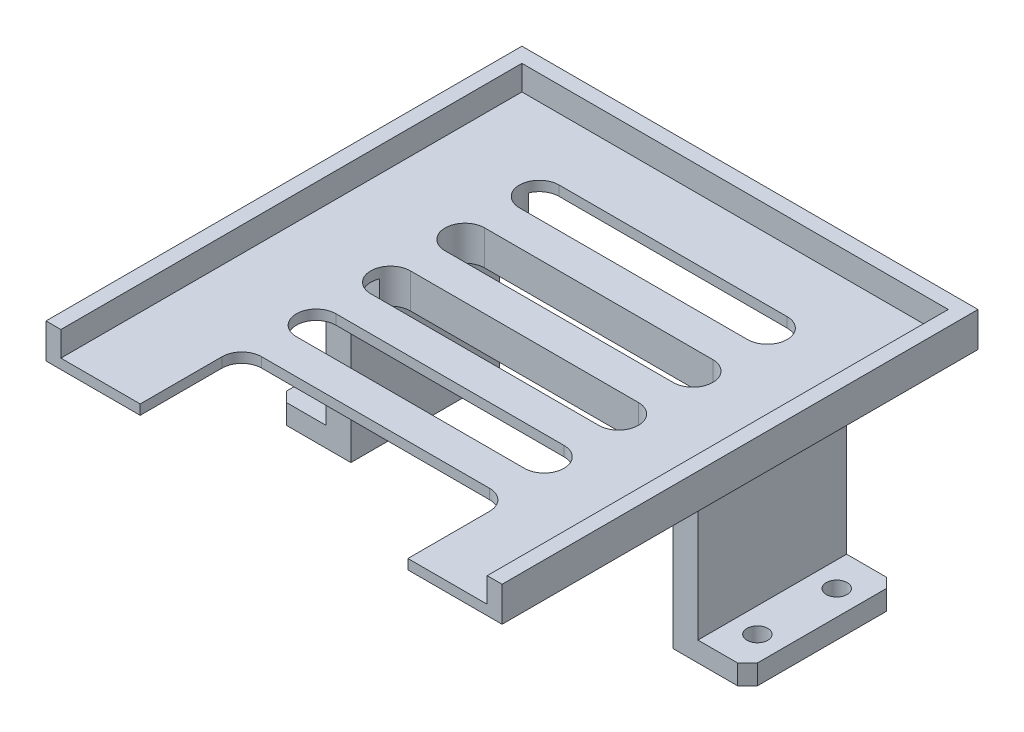
SolidWorks part; units mm, degrees
ref_plane "Front Plane" through (0, 0, 0) normal (0, 0, 1) x (1, 0, 0)
ref_plane "Top Plane" through (0, 0, 0) normal (0, 1, 0) x (1, 0, 0)
ref_plane "Right Plane" through (0, 0, 0) normal (1, 0, 0) x (0, 0, -1)
sketch "Sketch1" plane through (0, 0, 0) normal (0, 0, 1) x (1, 0, 0)
  line L0 (0, 17.5) -> (0, -17.5) construction
  line L1 (-37.5, -17.5) -> (37.5, -17.5)
  line L2 (-37.5, -12.5) -> (-37.5, 17.5)
  line L3 (-37.5, 17.5) -> (37.5, 17.5)
  line L4 (37.5, -12.5) -> (37.5, 17.5)
  line L5 (-37.5, -17.5) -> (37.5, 17.5) construction
  line L6 (-37.5, 17.5) -> (37.5, -17.5) construction
  line L7 (-37.5, -12.5) -> (-57.5, -12.5)
  line L8 (-32.5, -17.5) -> (32.5, -17.5)
  line L9 (-32.5, -17.5) -> (-32.5, 12.5)
  line L10 (-32.5, 12.5) -> (32.5, 12.5)
  line L11 (32.5, -17.5) -> (32.5, 12.5)
  line L12 (37.5, -17.5) -> (57.5, -17.5)
  line L14 (37.5, -12.5) -> (57.5, -12.5)
  line L15 (57.5, -17.5) -> (57.5, -12.5)
  line L16 (-57.5, -17.5) -> (-57.5, -12.5)
  line L17 (-37.5, -17.5) -> (-57.5, -17.5)
  point P0 (0, 0)
  dimension "D1" = 35
  dimension "D2" = 75
  dimension "D3" = 5
  dimension "D4" = 5
  dimension "D5" = 5
  dimension "D6" = 5
  dimension "D7" = 20
extrude "Boss-Extrude1" add sketch "Sketch1" along normal blind 30 contours L17 L1 L9 L10 L11 L12 L15 L14 L4 L3 L2 L7 L16
sketch "Sketch2" plane through (0, 17.5, 0) normal (0, 1, 0) x (1, 0, 0)
  line L0 (-37.5, -15) -> (37.5, -15) construction
  line L1 (-37.5, -30) -> (-37.5, 0) construction
  line L2 (37.5, -30) -> (37.5, 0) construction
  line L3 (0, 0) -> (0, -30) construction
  line L4 (-37.5, -30) -> (37.5, -30) construction
  line L6 (-25, -25) -> (25, -25)
  line L7 (-25, -25) -> (-25, -5)
  line L8 (-25, -5) -> (25, -5)
  line L9 (25, -25) -> (25, -5)
  line L10 (-25, -25) -> (25, -5) construction
  line L11 (-25, -5) -> (25, -25) construction
  point P11 (0, -15)
  dimension "D1" = 50
  dimension "D2" = 20
extrude "Cut-Extrude1" cut sketch "Sketch2" against normal blind 30
chamfer "Chamfer1" distance 2 angle 45 2 edges at (37.5, 17.5, 15) (-37.5, 17.5, 15)
sketch "Sketch3" plane through (0, -12.5, 0) normal (0, 1, 0) x (1, 0, 0)
  line L0 (-47.5, 0) -> (-47.5, -30) construction
  line L1 (-37.5, 0) -> (-57.5, 0) construction
  line L2 (-37.5, -30) -> (-57.5, -30) construction
  line L3 (47.5, 0) -> (47.5, -30) construction
  line L4 (37.5, 0) -> (57.5, 0) construction
  line L5 (37.5, -30) -> (57.5, -30) construction
  circle A0 centre (-47.5, -15) radius 2.1
  circle A1 centre (47.5, -15) radius 2.1
  dimension "D1" = 4.2
  dimension "D2" = 4.2
extrude "Cut-Extrude2" cut sketch "Sketch3" against normal blind 30
sketch "Sketch6" plane through (0, 17.5, 0) normal (0, 1, 0) x (1, 0, 0)
  line L0 (0, 0) -> (0, -30) construction
  line L1 (-35.5, -30) -> (35.5, -30) construction
  line L2 (-35.5, 0) -> (35.5, 0) construction
  line L3 (-2.5, -30) -> (2.5, -30)
  line L4 (-2.5, -30) -> (-2.5, 0)
  line L5 (-2.5, 0) -> (2.5, 0)
  line L6 (2.5, -30) -> (2.5, 0)
  line L7 (-2.5, -30) -> (2.5, 0) construction
  line L8 (-2.5, 0) -> (2.5, -30) construction
  point P5 (0, -15)
  dimension "D1" = 5
extrude "Boss-Extrude2" add sketch "Sketch6" against normal up to surface (5 mm away) up to face at (0, 12.5, 15)
sketch "Sketch8" plane through (0, 17.5, 0) normal (0, 1, 0) x (1, 0, 0)
  line L1 (-25, -5) -> (25, -5)
  line L2 (-25, -5) -> (-25, -25)
  line L3 (-25, -25) -> (25, -25)
  line L4 (25, -5) -> (25, -25)
extrude "Boss-Extrude3" add sketch "Sketch8" against normal up to surface (5 mm away) up to face at (13.75, 12.5, 15)
sketch "Sketch9" plane through (0, -17.5, 0) normal (0, -1, 0) x (-1, 0, 0)
  line L1 (57.5, -30) -> (32.5, -30)
  line L2 (57.5, -30) -> (57.5, 0)
  line L3 (57.5, 0) -> (32.5, 0)
  line L4 (32.5, -30) -> (32.5, 0)
extrude "Boss-Extrude4" add sketch "Sketch9" against normal up to surface (5 mm away) up to face at (-47.5, -12.5, 17.1)
sketch "Sketch10" plane through (0, -17.5, 0) normal (0, -1, 0) x (-1, 0, 0)
  line L1 (-32.5, -30) -> (-57.5, -30)
  line L2 (-32.5, -30) -> (-32.5, 0)
  line L3 (-32.5, 0) -> (-57.5, 0)
  line L4 (-57.5, -30) -> (-57.5, 0)
extrude "Boss-Extrude5" add sketch "Sketch10" against normal up to surface (5 mm away) up to face at (47.5, -12.5, 17.1)
sketch "Sketch12" plane through (0, -12.5, 0) normal (0, 1, 0) x (1, 0, 0)
  line L0 (37.5, -30) -> (57.5, -30) construction
  line L1 (57.5, 0) -> (47.5, 0)
  line L2 (57.5, 0) -> (57.5, -30)
  line L3 (57.5, -30) -> (47.5, -30)
  line L4 (47.5, 0) -> (47.5, -30)
  line L5 (0, -30) -> (0, 0) construction
  line L6 (-35.5, -30) -> (35.5, -30) construction
  line L7 (-35.5, 0) -> (35.5, 0) construction
  line L8 (-57.5, -30) -> (-47.5, -30)
  line L9 (-47.5, 0) -> (-47.5, -30)
  line L10 (-57.5, 0) -> (-47.5, 0)
  line L11 (-57.5, 0) -> (-57.5, -30)
extrude "Cut-Extrude3" cut sketch "Sketch12" against normal blind 10 contours L8 L9 L10 L11 | L2 L1 L4 L3
sketch "Sketch13" plane through (0, -12.5, 0) normal (0, 1, 0) x (1, 0, 0)
  line L0 (42.5, 0) -> (42.5, -30) construction
  line L1 (37.5, 0) -> (47.5, 0) construction
  line L2 (37.5, -30) -> (47.5, -30) construction
  line L3 (-42.5, 0) -> (-42.5, -30) construction
  line L4 (-37.5, 0) -> (-47.5, 0) construction
  line L5 (-37.5, -30) -> (-47.5, -30) construction
  circle A0 centre (-42.5, -15) radius 2.1
  circle A1 centre (42.5, -15) radius 2.1
  dimension "D1" = 4.2
  dimension "D2" = 4.2
extrude "Cut-Extrude4" cut sketch "Sketch13" against normal blind 10
chamfer "Chamfer2" distance 2 angle 45 4 edges at (47.5, -15, 30) (47.5, -15, 0) (-47.5, -15, 30) (-47.5, -15, 0)
sketch "Sketch14" plane through (0, -12.5, 0) normal (0, 1, 0) x (1, 0, 0)
  line L1 (39.247, -8.5107) -> (45.892, -8.5107)
  line L2 (39.247, -8.5107) -> (39.247, -20.451)
  line L3 (39.247, -20.451) -> (45.892, -20.451)
  line L4 (45.892, -8.5107) -> (45.892, -20.451)
  line L5 (-45.7882, -10.795) -> (-38.7279, -10.795)
  line L6 (-45.7882, -10.795) -> (-45.7882, -19.205)
  line L7 (-45.7882, -19.205) -> (-38.7279, -19.205)
  line L8 (-38.7279, -10.795) -> (-38.7279, -19.205)
extrude "Boss-Extrude6" add sketch "Sketch14" against normal up to surface (5 mm away) up to face at (-40.4, -17.5, 15)
sketch "Sketch15" plane through (0, -12.5, 0) normal (0, 1, 0) x (1, 0, 0)
  line L0 (0, 0) -> (0, -30) construction
  line L1 (-37.5, -30) -> (-47.5, -30)
  line L2 (-37.5, -30) -> (-37.5, 0)
  line L3 (-37.5, 0) -> (-47.5, 0)
  line L4 (-47.5, -30) -> (-47.5, 0)
  line L5 (-35.5, -30) -> (35.5, -30) construction
  line L6 (37.5, 0) -> (47.5, 0)
  line L7 (47.5, -30) -> (47.5, 0)
  line L8 (37.5, -30) -> (47.5, -30)
  line L9 (37.5, -30) -> (37.5, 0)
  line L10 (-42.5, 0) -> (-42.5, -30) construction
  line L11 (42.5, 0) -> (42.5, -30) construction
  line L12 (-47.5, -15) -> (-37.5, -15) construction
  circle A0 centre (-42.5, -7) radius 2.1
  circle A1 centre (-42.5, -23) radius 2.1
  circle A2 centre (42.5, -23) radius 2.1
  circle A3 centre (42.5, -7) radius 2.1
  dimension "D1" = 4.2
  dimension "D2" = 8
extrude "Cut-Extrude5" cut sketch "Sketch15" against normal up to surface (5 mm away) contours A0 | A1 | A3 | A2 up to face at (-41.8333, -17.5, 15)
sketch "Sketch16" plane through (0, -17.5, 0) normal (0, -1, 0) x (1, 0, 0)
  circle A2 centre (42.5124, 6.9245) radius 2.1
  circle A3 centre (42.5408, 22.9245) radius 2.1
sketch "Sketch17" plane through (0, 17.5, 0) normal (0, 1, 0) x (1, 0, 0)
  line L0 (0, 15) -> (0, -78) construction
  line L1 (-43, -78) -> (-46, -78)
  line L5 (43, 15) -> (-43, 15)
  line L9 (43, -78) -> (-43, -78)
  line L12 (-43, 15) -> (-43, -78)
  line L13 (43, 15) -> (43, -78)
  line L14 (-43, -31.5) -> (43, -31.5) construction
  line L15 (43, -78) -> (46, -78)
  line L16 (-46, -81) -> (46, -81)
  line L17 (-46, -81) -> (-46, 18)
  line L18 (-46, 18) -> (46, 18)
  line L19 (46, -81) -> (46, 18)
  line L20 (-46, -81) -> (46, 18) construction
  line L21 (-46, 18) -> (46, -81) construction
  point P6 (0, -31.5)
  line M16 (35.5, -30) -> (35.5, 0)
  line M17 (35.5, 0) -> (-35.5, 0)
  line M18 (-35.5, 0) -> (-35.5, -30)
  line M19 (-35.5, -30) -> (35.5, -30)
  dimension "D1" = 86
  dimension "D2" = 93
  dimension "D3" = 3
  dimension "D4" = 3
extrude "Boss-Extrude7" add sketch "Sketch17" along normal blind 2 contours L13 L5 L12 L9 M16 M19 M18 M17 | M19 M16 M17 M18
sketch "Sketch18" plane through (0, 19.5, 0) normal (0, 1, 0) x (1, 0, 0)
  line L0 (-46, 18) -> (-46, -78)
  line L1 (-46, -78) -> (-43, -78)
  line L2 (-43, -78) -> (-43, 15)
  line L3 (-43, 15) -> (43, 15)
  line L4 (43, 15) -> (43, -78)
  line L5 (43, -78) -> (46, -78)
  line L6 (46, -78) -> (46, 18)
  line L7 (46, 18) -> (-46, 18)
extrude "Boss-Extrude8" add sketch "Sketch18" along normal blind 5 and the other way blind 2
sketch "Sketch19" plane through (0, 19.5, 0) normal (0, 1, 0) x (1, 0, 0)
  line L0 (-43, -31.5) -> (43, -31.5) construction
  line L1 (-43, -16.5) -> (43, -16.5) construction
  line L2 (-43, 15) -> (-43, -78) construction
  line L3 (43, 15) -> (43, -78) construction
  line L4 (-43, -1.5) -> (43, -1.5) construction
  line L5 (-23, 15) -> (-23, -31.5) construction
  line L6 (43, 15) -> (-43, 15) construction
  line L7 (23, 15) -> (23, -31.5) construction
  line L8 (-23, -1.5) -> (23, -1.5) construction
  line L9 (-23, 2.5) -> (23, 2.5)
  line L10 (-23, -5.5) -> (23, -5.5)
  line L11 (-23, -16.5) -> (23, -16.5) construction
  line L12 (-23, -12.5) -> (23, -12.5)
  line L13 (-23, -20.5) -> (23, -20.5)
  line L14 (-23, -31.5) -> (23, -31.5) construction
  line L15 (-23, -27.5) -> (23, -27.5)
  line L16 (-23, -35.5) -> (23, -35.5)
  line L17 (-23, -46.5) -> (23, -46.5) construction
  line L18 (-23, -50.5) -> (23, -50.5)
  line L19 (-23, -42.5) -> (23, -42.5)
  line L20 (-23, -61.5) -> (23, -61.5) construction
  line L21 (-23, -65.5) -> (23, -65.5)
  line L22 (-23, -57.5) -> (23, -57.5)
  arc A0 (-23, 2.5) -> (-23, -5.5) centre (-23, -1.5) ccw
  arc A1 (23, -5.5) -> (23, 2.5) centre (23, -1.5) ccw
  arc A2 (-23, -12.5) -> (-23, -20.5) centre (-23, -16.5) ccw
  arc A3 (23, -20.5) -> (23, -12.5) centre (23, -16.5) ccw
  arc A4 (-23, -27.5) -> (-23, -35.5) centre (-23, -31.5) ccw
  arc A5 (23, -35.5) -> (23, -27.5) centre (23, -31.5) ccw
  arc A6 (-23, -50.5) -> (-23, -42.5) centre (-23, -46.5) cw
  arc A7 (23, -42.5) -> (23, -50.5) centre (23, -46.5) cw
  arc A8 (-23, -65.5) -> (-23, -57.5) centre (-23, -61.5) cw
  arc A9 (23, -57.5) -> (23, -65.5) centre (23, -61.5) cw
  point P20 (0, -1.5)
  point P27 (0, -16.5)
  point P32 (0, -31.5)
  point P39 (0, -46.5)
  point P46 (0, -61.5)
  dimension "D5" = 4
  dimension "D8" = 4
  dimension "D11" = 4
  dimension "D1" = 15
  dimension "D2" = 15
  dimension "D3" = 20
  dimension "D4" = 20
  dimension "D6" = 20
  dimension "D7" = 20
  dimension "D9" = 20
  dimension "D10" = 20
extrude "Cut-Extrude7" cut sketch "Sketch19" against normal blind 18
sketch "Sketch21" plane through (0, -12.5, 0) normal (0, 1, 0) x (1, 0, 0)
  line L0 (-37.5, 0) -> (-37.5, -30)
  line L1 (-37.5, -30) -> (-45.5, -30)
  line L2 (-45.5, -30) -> (-47.5, -28)
  line L3 (-47.5, -28) -> (-47.5, -2)
  line L4 (-47.5, -2) -> (-45.5, 0)
  line L5 (-45.5, 0) -> (-37.5, 0)
  line L6 (37.5, 0) -> (37.5, -30)
  line L7 (37.5, -30) -> (45.5, -30)
  line L8 (45.5, -30) -> (47.5, -28)
  line L9 (47.5, -28) -> (47.5, -2)
  line L10 (47.5, -2) -> (45.5, 0)
  line L11 (45.5, 0) -> (37.5, 0)
extrude "Cut-Extrude8" cut sketch "Sketch21" against normal blind 1
sketch "Sketch22" plane through (0, 19.5, 0) normal (0, 1, 0) x (1, 0, 0)
  line L0 (-27, -61.5) -> (-27, -78)
  line L1 (43, -78) -> (-43, -78) construction
  line L2 (27, -61.5) -> (27, -78)
  line L3 (27, -78) -> (-27, -78)
  line L4 (-27, -61.5) -> (27, -61.5)
  arc A0 (-23, -57.5) -> (-23, -65.5) centre (-23, -61.5) ccw construction
  arc A1 (23, -65.5) -> (23, -57.5) centre (23, -61.5) ccw construction
extrude "Cut-Extrude9" cut sketch "Sketch22" against normal blind 10
